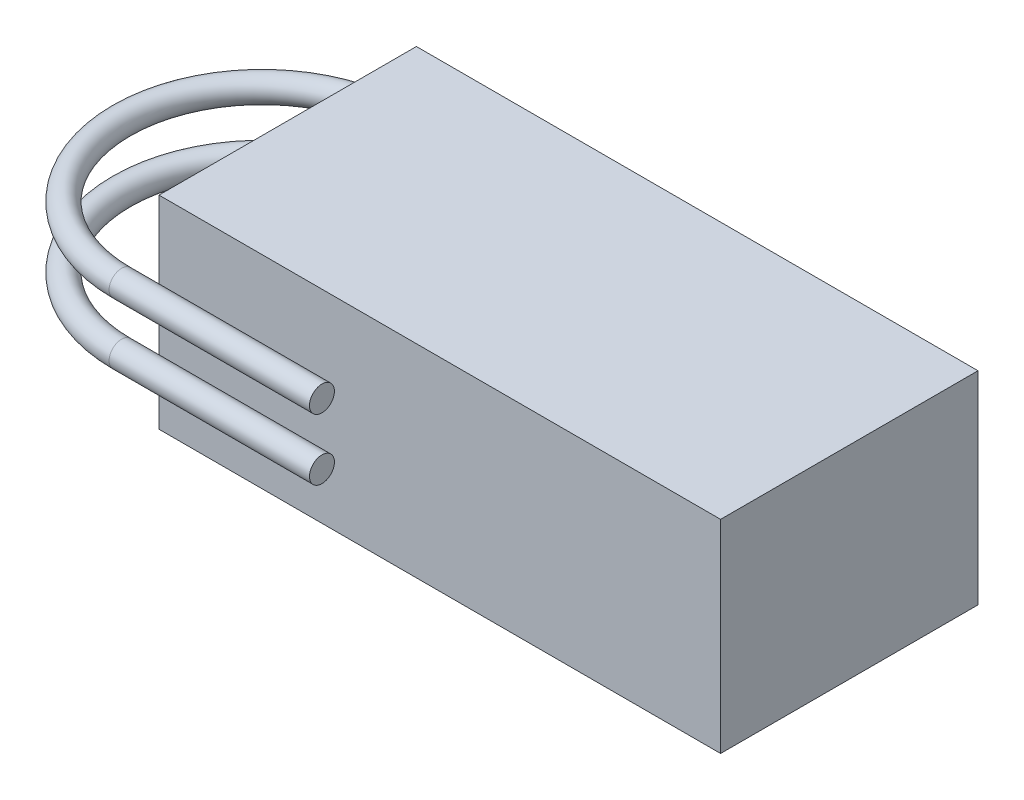
SolidWorks part; units mm, degrees
ref_plane "Plan de face" through (0, 0, 0) normal (0, 0, 1) x (1, 0, 0)
ref_plane "Plan de dessus" through (0, 0, 0) normal (0, 1, 0) x (1, 0, 0)
ref_plane "Plan de droite" through (0, 0, 0) normal (1, 0, 0) x (0, 0, -1)
sketch "Esquisse1" plane through (0, 0, 0) normal (0, 1, 0) x (1, 0, 0)
  line L1 (-36, -16.5) -> (36, -16.5)
  line L2 (-36, -16.5) -> (-36, 16.5)
  line L3 (-36, 16.5) -> (36, 16.5)
  line L4 (36, -16.5) -> (36, 16.5)
  line L5 (-36, -16.5) -> (36, 16.5) construction
  line L6 (-36, 16.5) -> (36, -16.5) construction
  point P0 (0, 0)
  dimension "D1" = 72
  dimension "D2" = 33
extrude "Boss.-Extru.1" add sketch "Esquisse1" along normal blind 26
sketch "Esquisse3" plane through (-10.3108, 0, 0) normal (-1, 0, 0) x (0, 0, 1)
  circle A1 centre (21.3002, 18.6743) radius 1.6 construction
  circle A2 centre (21.3002, 18.6743) radius 1.6
  circle A3 centre (21.3002, 10.8073) radius 1.6 construction
  circle A4 centre (21.3002, 10.8073) radius 1.6
extrude "Boss.-Extru.2" add sketch "Esquisse3" along normal up to surface (25.6892 mm away) separate body up to face at (-36, 13, 0)
sketch "Esquisse4" plane through (-36, 0, 0) normal (-1, 0, 0) x (0, 0, 1)
  line L0 (-14.75, 26) -> (-14.75, 0) construction
  line L3 (-16.5, 26) -> (16.5, 26) construction
  line L4 (-16.5, 0) -> (16.5, 0) construction
  line L5 (-16.5, 26) -> (-16.5, 0) construction
  line L6 (3.3002, 26) -> (3.3002, 0) construction
  circle A0 centre (21.3002, 18.6743) radius 1.6 construction
  circle A1 centre (21.3002, 10.8073) radius 1.6 construction
  circle A2 centre (21.3002, 18.6743) radius 1.6
  circle A3 centre (21.3002, 10.8073) radius 1.6
  dimension "D1" = 1.75
  dimension "D2" = 18
revolve "Révolution1" add sketch "Esquisse4" angle 180 about L6
